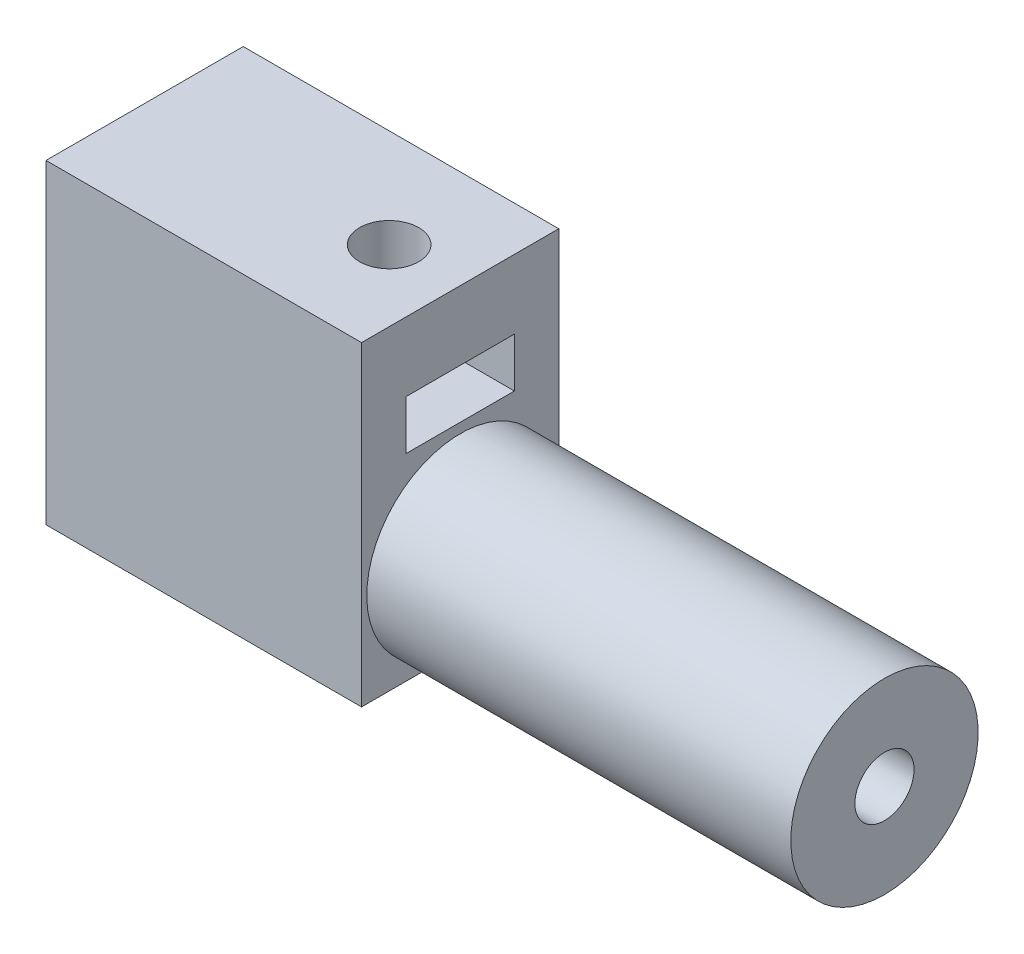
SolidWorks part; units mm, degrees
ref_plane "Front Plane" through (0, 0, 0) normal (0, 0, 1) x (1, 0, 0)
ref_plane "Top Plane" through (0, 0, 0) normal (0, 1, 0) x (1, 0, 0)
ref_plane "Right Plane" through (0, 0, 0) normal (1, 0, 0) x (0, 0, -1)
sketch "Sketch1" plane through (0, 0, 0) normal (0, 0, 1) x (1, 0, 0)
  line L1 (-8, 8) -> (8, 8)
  line L2 (-8, 8) -> (-8, -8)
  line L3 (-8, -8) -> (8, -8)
  line L4 (8, 8) -> (8, -8)
  line L5 (-8, 8) -> (8, -8) construction
  line L6 (-8, -8) -> (8, 8) construction
  point P0 (0, 0)
  dimension "D1" = 16
  dimension "D2" = 16
extrude "Boss-Extrude1" add sketch "Sketch1" along normal blind 10
sketch "Sketch2" plane through (-8, 0, 0) normal (-1, 0, 0) x (0, 0, 1)
  line L0 (10, -8) -> (0, -8) construction
  line L1 (10, 8) -> (0, 8) construction
  circle A0 centre (5, -3.97) radius 1.5
  point P6 (5, -8)
  dimension "D1" = 3
  dimension "D3" = 11.97
  dimension "D2" = 0
extrude "Cut-Extrude1" cut sketch "Sketch2" against normal blind 6
sketch "Sketch3" plane through (0, 8, 0) normal (0, 1, 0) x (1, 0, 0)
  line L0 (8, -10) -> (8, 0) construction
  line L1 (-8, -10) -> (-8, 0) construction
  circle A0 centre (4.4, -5) radius 1.5
  point P6 (8, -5)
  dimension "D3" = 3
  dimension "D1" = 0
  dimension "D2" = 12.4
extrude "Cut-Extrude2" cut sketch "Sketch3" against normal blind 6
sketch "Sketch4" plane through (-8, 0, 0) normal (-1, 0, 0) x (0, 0, 1)
  line L1 (7.75, -2.3823) -> (5, -0.7946)
  line L2 (5, -0.7946) -> (2.25, -2.3823)
  line L3 (2.25, -2.3823) -> (2.25, -5.5577)
  line L4 (2.25, -5.5577) -> (5, -7.1454)
  line L5 (5, -7.1454) -> (7.75, -5.5577)
  line L6 (7.75, -5.5577) -> (7.75, -2.3823)
  circle A0 centre (5, -3.97) radius 2.75 construction
  dimension "D1" = 5.5
extrude "Cut-Extrude3" cut sketch "Sketch4" against normal blind 2.5 from offset 3.5 offset against normal yes
sketch "Sketch6" plane through (-8, 0, 0) normal (-1, 0, 0) x (0, 0, 1)
  line L0 (10, -8) -> (0, -8) construction
  line L1 (2.25, -12.03) -> (7.75, -12.03)
  line L2 (2.25, -12.03) -> (2.25, -3.97)
  line L3 (2.25, -3.97) -> (7.75, -3.97)
  line L4 (7.75, -12.03) -> (7.75, -3.97)
  line L5 (2.25, -12.03) -> (7.75, -3.97) construction
  line L6 (2.25, -3.97) -> (7.75, -12.03) construction
  circle A0 centre (5, -3.97) radius 1.5 construction
  point P0 (5, -8)
  dimension "D1" = 2.75
  dimension "D2" = 0
extrude "Cut-Extrude5" cut sketch "Sketch6" against normal blind 2.5 from offset 3.5 offset against normal yes
sketch "Sketch7" plane through (0, 8, 0) normal (0, 1, 0) x (1, 0, 0)
  line L0 (8, -10) -> (8, 0) construction
  line L1 (7.5747, -5.0699) -> (6.0479, -2.2856)
  line L2 (6.0479, -2.2856) -> (2.8732, -2.2157)
  line L3 (2.8732, -2.2157) -> (1.2253, -4.9301)
  line L4 (1.2253, -4.9301) -> (2.7521, -7.7144)
  line L5 (2.7521, -7.7144) -> (5.9268, -7.7843)
  line L6 (5.9268, -7.7843) -> (7.5747, -5.0699)
  line L8 (11.5395, -7.7493) -> (4.4605, -7.7493)
  line L9 (11.5395, -7.7493) -> (11.5395, -2.2507)
  line L10 (11.5395, -2.2507) -> (4.4605, -2.2507)
  line L11 (4.4605, -7.7493) -> (4.4605, -2.2507)
  line L12 (11.5395, -7.7493) -> (4.4605, -2.2507) construction
  line L13 (11.5395, -2.2507) -> (4.4605, -7.7493) construction
  circle A0 centre (4.4, -5) radius 2.75 construction
  point P11 (8, -5)
  circle M1 centre (4.4, -5) radius 1.5
  line M5 (8, -10) -> (8, 0)
  dimension "D1" = 5.5
extrude "Cut-Extrude6" cut sketch "Sketch7" against normal blind 2.5 from offset 3.5 contours L10 L1 L6 L8 M5 | L11 L5 L6 L1 L2 M1 | L5 L11 L2 L3 L4 M1 | L9 L10 L8 M5 offset against normal yes
sketch "Sketch9" plane through (8, 0, 0) normal (1, 0, 0) x (0, 0, -1)
  line L0 (-10, -8) -> (0, -8) construction
  circle A0 centre (-4.9855, -3.25) radius 4.75
  dimension "D1" = 9.5
  dimension "D2" = 4.75
extrude "Boss-Extrude2" add sketch "Sketch9" along normal blind 21.5
sketch "Sketch10" plane through (29.5, 0, 0) normal (1, 0, 0) x (0, 0, -1)
  circle A0 centre (-4.9855, -3.25) radius 1.5
  dimension "D1" = 3
extrude "Cut-Extrude7" cut sketch "Sketch10" against normal blind 6
sketch "Sketch11" plane through (29.5, 0, 0) normal (1, 0, 0) x (0, 0, -1)
  line L1 (-5.1298, -0.0779) -> (-7.8048, -1.7889)
  line L2 (-7.8048, -1.7889) -> (-7.6605, -4.9611)
  line L3 (-7.6605, -4.9611) -> (-4.8411, -6.4221)
  line L4 (-4.8411, -6.4221) -> (-2.1661, -4.7111)
  line L5 (-2.1661, -4.7111) -> (-2.3105, -1.5389)
  line L6 (-2.3105, -1.5389) -> (-5.1298, -0.0779)
  line L7 (-7.7383, -12.875) -> (-2.2383, -12.875)
  line L8 (-7.7383, -12.875) -> (-7.7383, -3.125)
  line L9 (-7.7383, -3.125) -> (-2.2383, -3.125)
  line L10 (-2.2383, -12.875) -> (-2.2383, -3.125)
  line L11 (-7.7383, -12.875) -> (-2.2383, -3.125) construction
  line L12 (-7.7383, -3.125) -> (-2.2383, -12.875) construction
  circle A0 centre (-4.9855, -3.25) radius 2.75 construction
  circle A1 centre (-4.9855, -3.25) radius 4.75 construction
  point P1 (-4.9883, -8)
  dimension "D1" = 5.5
extrude "Cut-Extrude9" cut sketch "Sketch11" against normal blind 2.5 from offset 3.5 contours L7 L10 L2 L8 | L2 L10 L4 L3 L8 | L9 L2 L3 L4 L5 L1 | L2 L9 L1 L5 L6 offset against normal yes
equation "\"D2@Sketch9\"=\"D1@Sketch9\"/2"
